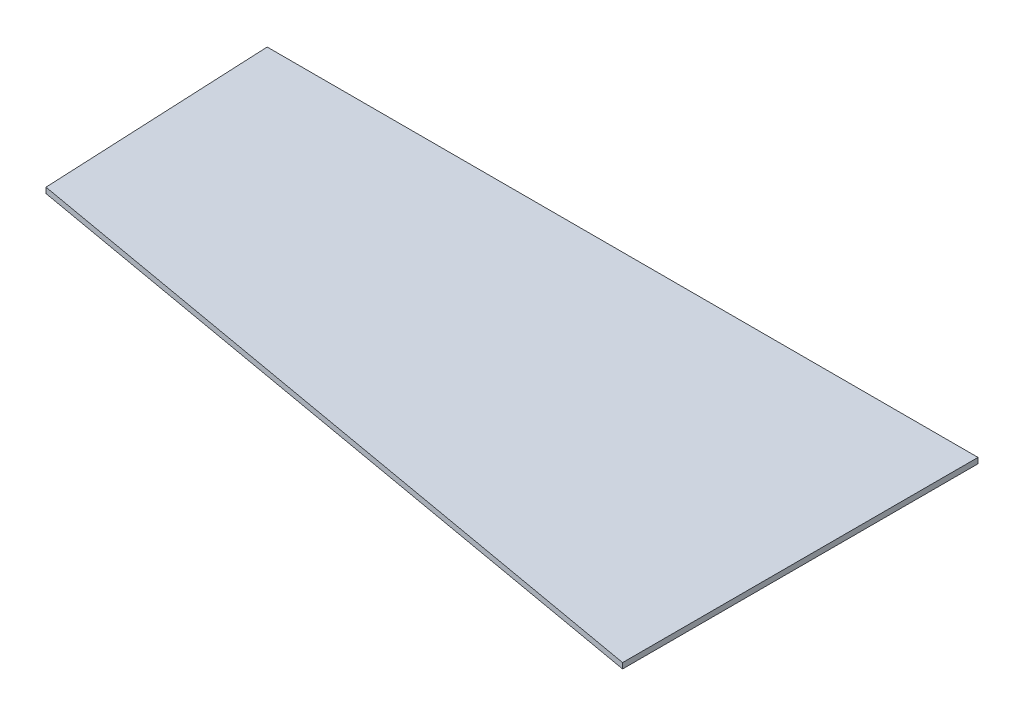
SolidWorks part; units mm, degrees
ref_plane "Front Plane" through (0, 0, 0) normal (0, 0, 1) x (1, 0, 0)
ref_plane "Top Plane" through (0, 0, 0) normal (0, 1, 0) x (1, 0, 0)
ref_plane "Right Plane" through (0, 0, 0) normal (1, 0, 0) x (0, 0, -1)
sketch "Sketch1" plane through (0, 0, 0) normal (0, 1, 0) x (1, 0, 0)
  line L0 (0, 0) -> (0, 1219.2)
  line L1 (0, 1219.2) -> (-2438.4, 1219.2)
  line L2 (-2438.4, 1219.2) -> (-2401.3552, 423.4237)
  line L3 (-2401.3552, 423.4237) -> (0, 0)
  point P3 (0, 0)
  point P6 (-2357.4199, 1219.2)
  dimension "D1" = 1219.2
  dimension "D2" = 2438.4
  dimension "D3" = 80
  dimension "D4" = 2438.4
extrude "Boss-Extrude1" add sketch "Sketch1" along normal blind 19.05 contours L3 L0 L1 L2
